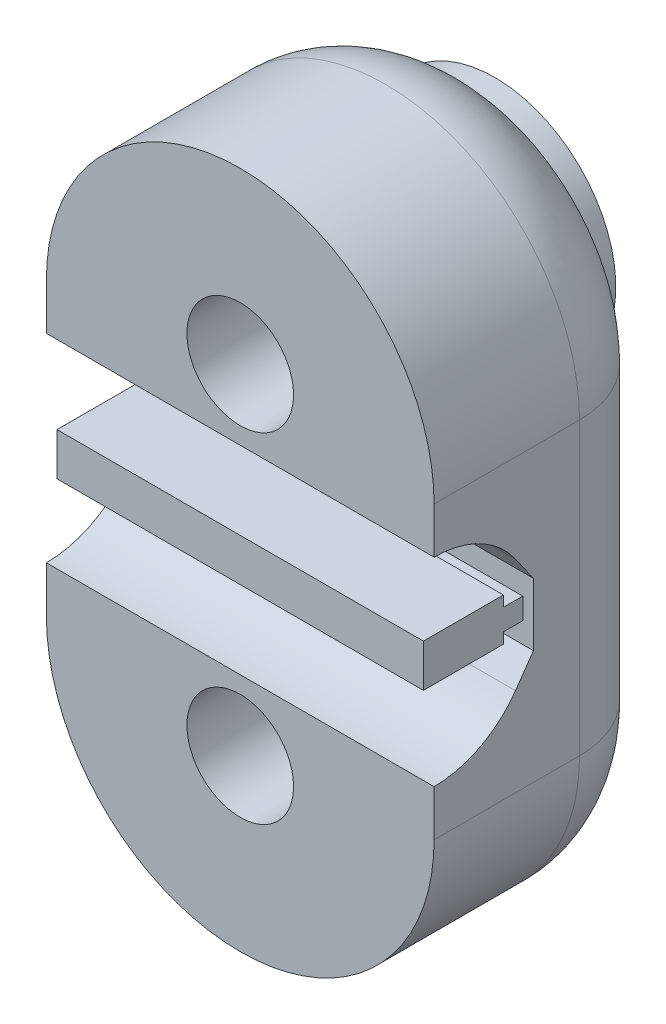
SolidWorks part; units mm, degrees
ref_plane "Front Plane" through (0, 0, 0) normal (0, 0, 1) x (1, 0, 0)
ref_plane "Top Plane" through (0, 0, 0) normal (0, 1, 0) x (1, 0, 0)
ref_plane "Right Plane" through (0, 0, 0) normal (1, 0, 0) x (0, 0, -1)
sketch "Sketch1" plane through (0, 0, 0) normal (0, 0, 1) x (1, 0, 0)
  line L1 (-5, 7.5) -> (-5, -4.5)
  line L3 (11, -4.5) -> (11, 7.5)
  arc A0 (11, 7.5) -> (-5, 7.5) centre (3, 7.5) ccw
  arc A1 (-5, -4.5) -> (11, -4.5) centre (3, -4.5) ccw
extrude "Boss-Extrude1" add sketch "Sketch1" along normal blind 10
sketch "Sketch4" plane through (-5, 0, 0) normal (-1, 0, 0) x (0, 0, 1)
  line L0 (10, -4.5) -> (10, 7.5) construction
  line L1 (10, 1.5) -> (10, 10.0583) construction
  line L2 (10, 1.5) -> (5.9, 1.5) construction
  line L3 (6.6415, -0.8517) -> (5.9, 0.2073)
  line L4 (6.6415, 3.8517) -> (5.9, 2.7927)
  line L5 (5.9, 0.2073) -> (5.9, 2.7927)
  arc A0 (6.6415, -0.8517) -> (6.6415, 3.8517) centre (10, 1.5) ccw
  dimension "D1" = 35
extrude "Cut-Extrude3" cut sketch "Sketch4" against normal through all
sketch "Sketch5" plane through (0, 0, 0) normal (0, 0, -1) x (-1, 0, 0)
  line L0 (5, -4.5) -> (5, 7.5) construction
  line L1 (-11, 1.5) -> (5, 1.5) construction
  line L2 (-11, -4.5) -> (-11, 7.5) construction
  line L3 (5, 7.5) -> (5, -4.5) construction
  circle A0 centre (-3, 8.5) radius 2.2
  circle A1 centre (-3, -5.5) radius 2.2
  dimension "D1" = 8
  dimension "D2" = 8
  dimension "D3" = 7
  dimension "D4" = 7
extrude "Cut-Extrude4" cut sketch "Sketch5" against normal through all
fillet "Fillet2" radius 4 4 edges at (11, 1.5, 0) (3, -12.5, 0) (-5, 1.5, 0) (3, 15.5, 0)
sketch "Sketch7" plane through (0, 0, 0) normal (0, 0, -1) x (-1, 0, 0)
  circle A0 centre (-3, 8.5) radius 5
  circle A1 centre (-3, -5.5) radius 5
  circle A2 centre (-3, 8.5) radius 2.2 construction
  circle A3 centre (-3, 8.5) radius 2.2
  circle A4 centre (-3, -5.5) radius 2.2 construction
  circle A5 centre (-3, -5.5) radius 2.2
extrude "Boss-Extrude2" add sketch "Sketch7" along normal blind 0.5 and the other way blind 3
sketch "Sketch8" plane through (0, 0, 5.9) normal (0, 0, 1) x (1, 0, 0)
  line L0 (-5.3498, 1.5) -> (11, 1.5) construction
  line L1 (11, 2.7927) -> (11, 0.2073) construction
  line L4 (-4.56, 2.7927) -> (-4.56, 0.2073)
  line L5 (-4.56, 1.94) -> (-4.56, 1.06)
  line L6 (-4.56, 1.06) -> (10.56, 1.06)
  line L7 (10.56, 2.7927) -> (10.56, 0.2073)
  line L8 (10.56, 1.94) -> (10.56, 1.06)
  line L9 (-4.56, 1.94) -> (10.56, 1.94)
  line L10 (-5.3498, 1.06) -> (11, 1.06) construction
  line L11 (-5.3498, 1.94) -> (11, 1.94) construction
  line L12 (11, 0.2073) -> (-5, 0.2073) construction
  dimension "D5" = 0
  dimension "D1" = 0.44
  dimension "D2" = 0.44
  dimension "D3" = 0.44
  dimension "D4" = 0.44
extrude "Boss-Extrude3" add sketch "Sketch8" along normal blind 0.8
sketch "Sketch9" plane through (0, 0, 6.7) normal (0, 0, 1) x (1, 0, 0)
  line L0 (-4.56, 1.5) -> (10.56, 1.5) construction
  line L1 (-4.56, 1.94) -> (-4.56, 1.06) construction
  line L2 (10.56, 1.06) -> (10.56, 1.94) construction
  line L3 (-4.56, 0.62) -> (10.56, 0.62)
  line L4 (-4.56, 2.38) -> (10.56, 2.38)
  line L5 (-4.56, 0.62) -> (-4.56, 2.38)
  line L6 (10.56, 0.62) -> (10.56, 2.38)
  dimension "D1" = 0.88
  dimension "D2" = 0.88
extrude "Boss-Extrude4" add sketch "Sketch9" along normal up to surface (3.3 mm away) up to face at (0.8, -5.5, 10)
